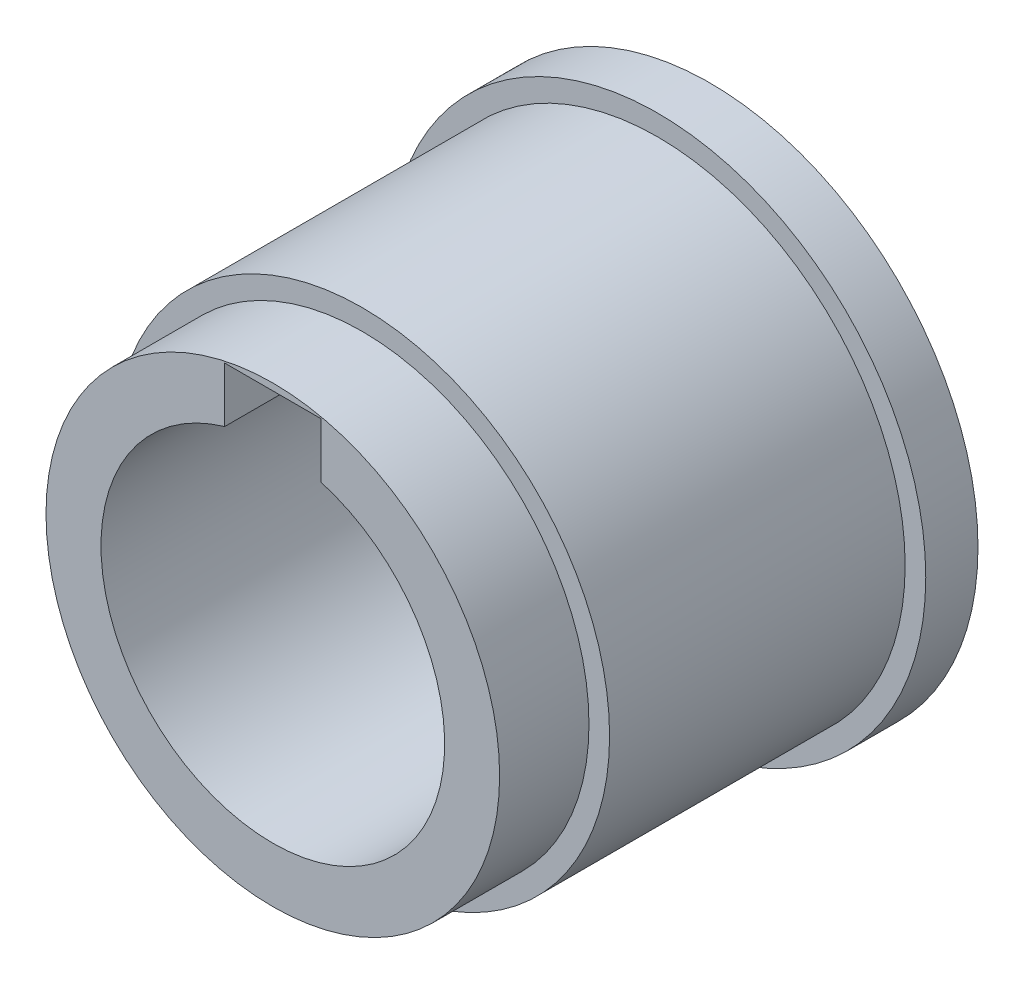
SolidWorks part; units mm, degrees
material "AISI 1020"
ref_plane "Спереди" through (0, 0, 0) normal (0, 0, 1) x (1, 0, 0)
ref_plane "Сверху" through (0, 0, 0) normal (0, 1, 0) x (1, 0, 0)
ref_plane "Справа" through (0, 0, 0) normal (1, 0, 0) x (0, 0, -1)
sketch "Эскиз1" plane through (0, 0, 0) normal (1, 0, 0) x (0, 0, -1)
  line L0 (23, 32.2445) -> (23, 15.5823) construction
  line L1 (26.8, 12.5) -> (-5, 12.5)
  line L2 (26.8, 12.5) -> (26.8, 19.5)
  line L3 (26.8, 19.5) -> (23, 19.5)
  line L4 (23, 19.5) -> (23, 18)
  line L5 (23, 18) -> (1.5, 18)
  line L6 (1.5, 18) -> (1.5, 16.5)
  line L7 (1.5, 16.5) -> (-5, 16.5)
  line L8 (-5, 16.5) -> (-5, 12.5)
  line L11 (-1000, 0) -> (49000, 0) construction
  line L12 (-5, 12) -> (-5, -12.5) construction
  line L13 (26.8, -12.5) -> (26.8, 12) construction
  line L14 (1.5, 15.5823) -> (1.5, 32.2445) construction
  dimension "D1" = 4
  dimension "D2" = 1.5
  dimension "D3" = 1.5
  dimension "D4" = 25
revolve "Повернуть1" add sketch "Эскиз1" angle 360 about L11
sketch "Эскиз2" plane through (0, 0, 5) normal (0, 0, 1) x (1, 0, 0)
  line L0 (-3.5, 12.5) -> (3.5, 12.5) construction
  line L1 (-3.5, 16) -> (3.5, 16)
  line L2 (-3.5, 16) -> (-3.5, 9)
  line L3 (-3.5, 9) -> (3.5, 9)
  line L4 (3.5, 16) -> (3.5, 9)
  circle A0 centre (0, 0) radius 12.5 construction
  point P4 (0, 9)
  dimension "D1" = 7
extrude "Вырез-Вытянуть1" cut sketch "Эскиз2" against normal through all
